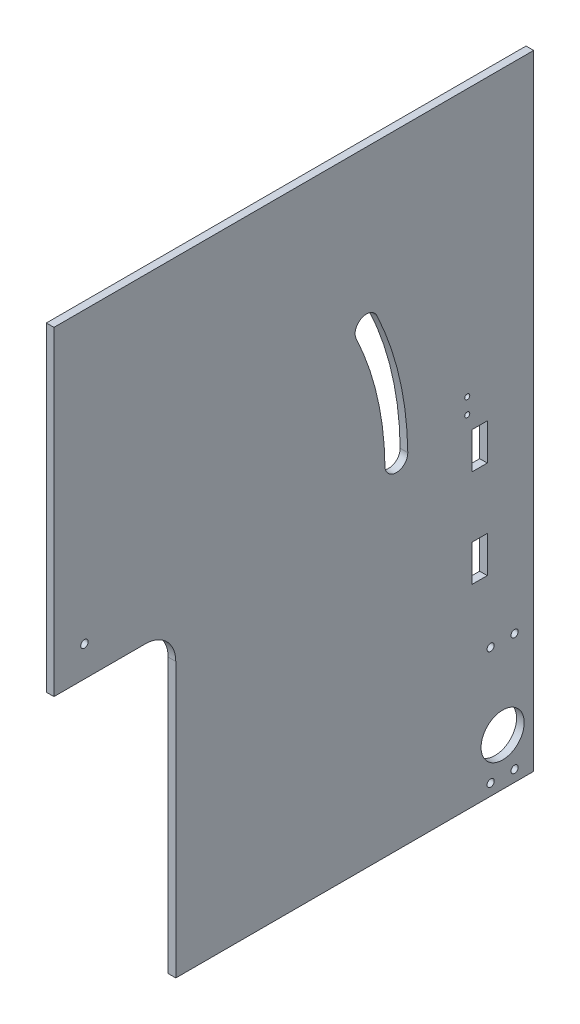
SolidWorks part; units mm, degrees
material "Acrylic (Medium-high impact)"
ref_plane "Front" through (0, 0, 0) normal (0, 0, 1) x (1, 0, 0)
ref_plane "Top" through (0, 0, 0) normal (0, 1, 0) x (1, 0, 0)
ref_plane "Right" through (0, 0, 0) normal (1, 0, 0) x (0, 0, -1)
sketch "Sketch1" plane through (0, 0, 0) normal (1, 0, 0) x (0, 0, -1)
  line L1 (-100.0125, 130.175) -> (100.0125, 130.175)
  line L2 (-100.0125, 130.175) -> (-100.0125, -130.175)
  line L3 (-100.0125, -130.175) -> (100.0125, -130.175)
  line L4 (100.0125, 130.175) -> (100.0125, -130.175)
  point P4 (-100.0125, 0)
  point P6 (0, 130.175)
  dimension "D1" = 260.35
  dimension "D2" = 200.025
extrude "Boss-Extrude1" add sketch "Sketch1" along normal blind 3.175
sketch "Sketch3" plane through (0, 0, 0) normal (-1, 0, 0) x (0, 0, 1)
  line L0 (-55.5625, 104.775) -> (77.7875, 104.775)
  line L1 (77.7875, 79.375) -> (-55.5625, 79.375)
  line L2 (-26.9875, 130.175) -> (-26.9875, -130.175) construction
  line L3 (-100.0125, 130.175) -> (100.0125, 130.175) construction
  line L4 (100.0125, -130.175) -> (-100.0125, -130.175) construction
  line L5 (100.0125, 130.175) -> (100.0125, -130.175) construction
  line L6 (-60.7375, 79.375) -> (-60.7375, 80.4772)
  line L12 (-55.5625, 92.075) -> (-68.2625, 92.075) construction
  arc A0 (77.7875, 104.775) -> (77.7875, 79.375) centre (77.7875, 92.075) cw
  arc A1 (-55.5625, 79.375) -> (-55.5625, 104.775) centre (-55.5625, 92.075) cw
  point P15 (90.4875, 92.075)
  dimension "D1" = 25.4
  dimension "D3" = 133.35
  dimension "D2" = 9.525
  dimension "D4" = 127
  dimension "D5" = 222.25
  dimension "D8" = 5.175
extrude "Cut-Extrude1" [suppressed] cut sketch "Sketch3" against normal through all contours A1 L1 A0 L0
sketch "Sketch6" plane through (3.175, 0, 0) normal (1, 0, 0) x (0, 0, -1)
  line L0 (117.5875, -88.265) -> (117.5875, -83.185)
  line L1 (139.5875, -83.185) -> (139.5875, -88.265)
  line L2 (111.5875, -103.765) -> (111.5875, -98.685)
  line L3 (114.5875, -103.765) -> (114.5875, -98.685)
  line L4 (111.5875, -72.765) -> (111.5875, -67.685)
  line L5 (114.5875, -72.765) -> (114.5875, -67.685)
  line L6 (128.5875, -83.185) -> (128.5875, -88.265) construction
  line L7 (145.5875, -103.765) -> (145.5875, -98.685)
  line L8 (142.5875, -103.765) -> (142.5875, -98.685)
  line L9 (142.5875, -72.765) -> (142.5875, -67.685)
  line L10 (145.5875, -72.765) -> (145.5875, -67.685)
  line L11 (-100.0125, 130.175) -> (-100.0125, -130.175) construction
  line L12 (-100.0125, -130.175) -> (100.0125, -130.175) construction
  arc A0 (117.5875, -88.265) -> (139.5875, -88.265) centre (128.5875, -88.265) ccw
  arc A1 (139.5875, -83.185) -> (117.5875, -83.185) centre (128.5875, -83.185) ccw
  arc A2 (111.5875, -103.765) -> (114.5875, -103.765) centre (113.0875, -103.765) ccw
  arc A3 (114.5875, -98.685) -> (111.5875, -98.685) centre (113.0875, -98.685) ccw
  arc A4 (111.5875, -72.765) -> (114.5875, -72.765) centre (113.0875, -72.765) ccw
  arc A5 (114.5875, -67.685) -> (111.5875, -67.685) centre (113.0875, -67.685) ccw
  arc A6 (145.5875, -103.765) -> (142.5875, -103.765) centre (144.0875, -103.765) cw
  arc A7 (142.5875, -98.685) -> (145.5875, -98.685) centre (144.0875, -98.685) cw
  arc A8 (145.5875, -72.765) -> (142.5875, -72.765) centre (144.0875, -72.765) cw
  arc A9 (142.5875, -67.685) -> (145.5875, -67.685) centre (144.0875, -67.685) cw
  circle A10 centre (113.0875, -69.36) radius 3.175
  circle A11 centre (144.0875, -69.36) radius 3.175
  circle A12 centre (113.0875, -102.09) radius 3.175
  circle A13 centre (144.0875, -102.09) radius 3.175
  point P37 (128.5875, -85.725)
  point P38 (139.5875, -85.725)
  dimension "D5" = 1.5
  dimension "D9" = 1.5
  dimension "D12" = 6.35
  dimension "D1" = 5.08
  dimension "D2" = 5.08
  dimension "D3" = 15.5
  dimension "D4" = 15.5
  dimension "D6" = 15.5
  dimension "D7" = 15.5
  dimension "D8" = 5.08
  dimension "D10" = 228.6
  dimension "D11" = 44.45
sketch "Sketch8" plane through (0, 0, 0) normal (-1, 0, 0) x (0, 0, 1)
  line L0 (100.0125, 130.175) -> (100.0125, -130.175) construction
  line L1 (100.0125, -130.175) -> (-100.0125, -130.175) construction
  line L3 (100.0125, -130.175) -> (-100.0125, -130.175) construction
  circle A0 centre (87.3125, 9.525) radius 1.55
  circle A5 centre (-72.3175, 18.925) radius 1.05
  circle A6 centre (-72.3175, 12.425) radius 1.05
  point P11 (-63.8175, 22.225)
  dimension "D1" = 3.1
  dimension "D15" = 3.3
  dimension "D8" = 2.1
  dimension "D2" = 12.7
  dimension "D3" = 139.7
  dimension "D6" = 151.13
  dimension "D7" = 152.4
  dimension "D9" = 6.5
  dimension "D12" = 8.5
extrude "Cut-Extrude7" cut sketch "Sketch8" against normal through all
sketch "Sketch9" plane through (0, 0, 0) normal (-1, 0, 0) x (0, 0, 1)
  line L0 (100.0125, 130.175) -> (100.0125, -130.175) construction
  line L1 (100.0125, -3.175) -> (49.2125, -3.175)
  line L2 (100.0125, -3.175) -> (100.0125, -130.175)
  line L3 (100.0125, -130.175) -> (49.2125, -130.175)
  line L4 (49.2125, -3.175) -> (49.2125, -130.175)
  line L5 (100.0125, -130.175) -> (-100.0125, -130.175) construction
  dimension "D1" = 50.8
  dimension "D2" = 127
extrude "Cut-Extrude8" cut sketch "Sketch9" against normal through all
fillet "Fillet1" radius 12.7 1 edges at (1.5875, -3.175, 49.2125)
sketch "Sketch10" plane through (0, 0, 0) normal (-1, 0, 0) x (0, 0, 1)
  line L4 (-42.8232, -130.175) -> (-42.8232, 6.325) construction
  line L5 (49.2125, -130.175) -> (-100.0125, -130.175) construction
  arc A9 (-28.2913, 69.3688) -> (-42.8232, 6.325) centre (87.3125, 9.525) ccw construction
  arc A10 (-34.6312, 67.0954) -> (-47.5281, 11.1443) centre (87.3125, 9.525) ccw
  arc A11 (-26.0179, 63.0289) -> (-38.0038, 11.03) centre (87.3125, 9.525) ccw
  arc A12 (-47.5281, 11.1443) -> (-38.0038, 11.03) centre (-42.766, 11.0872) ccw
  arc A13 (-34.6312, 67.0954) -> (-26.0179, 63.0289) centre (-30.3245, 65.0622) cw
  circle A14 centre (87.3125, 9.525) radius 125.3254 construction
  circle A15 centre (87.3125, 9.525) radius 130.175 construction
  circle A16 centre (87.3125, 9.525) radius 134.8504 construction
  point P23 (-28.2913, 69.3688)
  dimension "D1" = 4.7625
  dimension "D2" = 136.5
  dimension "D4" = 260.35
  dimension "D3" = 53.975
extrude "Cut-Extrude9" cut sketch "Sketch10" against normal through all
sketch "Sketch14" plane through (3.175, 0, 0) normal (1, 0, 0) x (0, 0, -1)
  line L0 (36.5125, -130.175) -> (36.5125, 130.175) construction
  line L5 (-49.2125, -130.175) -> (100.0125, -130.175) construction
  line L6 (100.0125, 130.175) -> (-100.0125, 130.175) construction
  line L7 (-100.0125, 130.175) -> (-100.0125, -3.175) construction
  line L14 (65.0875, -120.523) -> (65.0875, -126.873) construction
  circle A0 centre (-87.3125, 9.525) radius 181.0945 construction
  arc A1 (27.1013, -128.905) -> (33.4472, -122.7825) centre (27.1013, -122.555) ccw construction
  circle A2 centre (65.0875, -126.873) radius 1.5
  circle A3 centre (65.0875, -120.523) radius 1.5
  dimension "D6" = 3
  dimension "D7" = 6.35
  dimension "D1" = 136.525
  dimension "D8" = 3.302
  dimension "D9" = 28.575
extrude "Cut-Extrude11" [suppressed] cut sketch "Sketch14" against normal through all
sketch "Sketch15" plane through (3.175, 0, 0) normal (1, 0, 0) x (0, 0, -1)
  line L1 (74.3175, 6.075) -> (80.6675, 6.075)
  line L2 (74.3175, 6.075) -> (74.3175, -9.165)
  line L3 (74.3175, -9.165) -> (80.6675, -9.165)
  line L4 (80.6675, 6.075) -> (80.6675, -9.165)
  line L11 (74.3175, -34.565) -> (80.6675, -34.565)
  line L12 (74.3175, -34.565) -> (74.3175, -49.805)
  line L13 (74.3175, -49.805) -> (80.6675, -49.805)
  line L14 (80.6675, -34.565) -> (80.6675, -49.805)
  circle A0 centre (72.3175, 12.425) radius 1.05 construction
  dimension "D4" = 2
  dimension "D1" = 6.35
  dimension "D2" = 15.24
  dimension "D3" = 25.4
  dimension "D5" = 6.35
extrude "Cut-Extrude12" cut sketch "Sketch15" against normal through all
sketch "Sketch16" plane through (3.175, 0, 0) normal (1, 0, 0) x (0, 0, -1)
  line L0 (82.075, -76.4125) -> (92.075, -76.4125) construction
  line L1 (82.075, -76.4125) -> (82.075, -125.4125) construction
  line L2 (92.075, -76.4125) -> (92.075, -125.4125) construction
  line L3 (82.075, -125.4125) -> (92.075, -125.4125) construction
  line L4 (100.0125, -130.175) -> (100.0125, 130.175) construction
  line L6 (87.075, -125.4125) -> (87.075, -110.5625) construction
  line L7 (87.075, -119.5625) -> (68.66, -119.5625) construction
  line L9 (-49.2125, -130.175) -> (100.0125, -130.175) construction
  circle A0 centre (82.075, -125.4125) radius 1.5
  circle A1 centre (82.075, -76.4125) radius 1.5
  circle A2 centre (92.075, -125.4125) radius 1.5
  circle A3 centre (92.075, -76.4125) radius 1.5
  circle A4 centre (87.075, -110.5625) radius 9
  dimension "D1" = 3
  dimension "D7" = 18
  dimension "D2" = 10
  dimension "D3" = 49
  dimension "D4" = 14.85
  dimension "D5" = 7.9375
  dimension "D6" = 4.7625
extrude "Cut-Extrude13" cut sketch "Sketch16" against normal through all
equation "\"bottomThickness\"= .220in"
equation "\"wallThickness\"= .125in"
equation "\"D1@Boss-Extrude1\"=\"wallThickness\""
